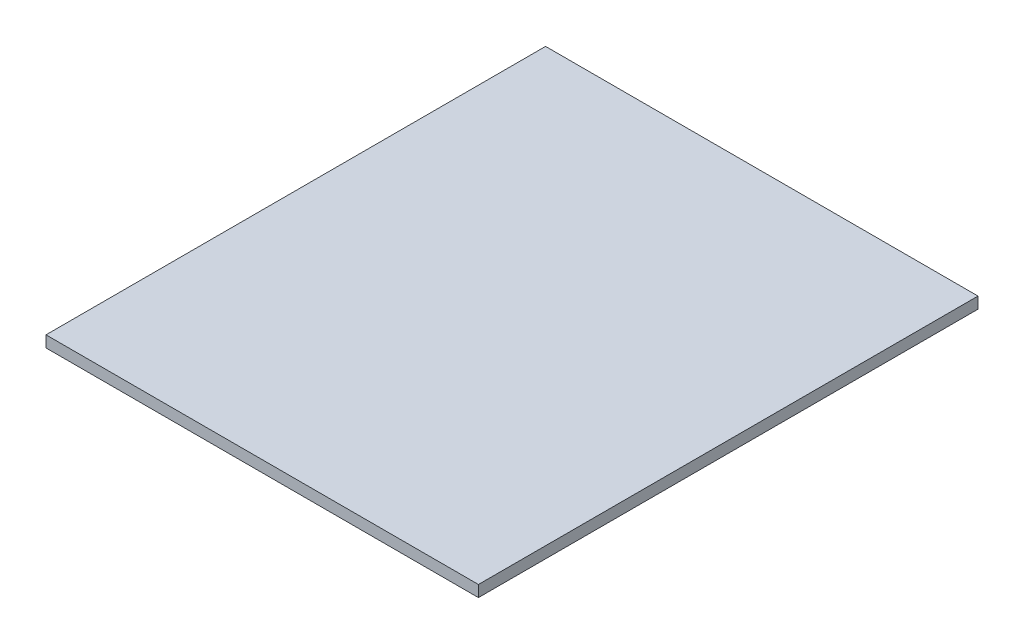
SolidWorks part; units mm, degrees
material "6061 Alloy"
ref_plane "Front Plane" through (0, 0, 0) normal (0, 0, 1) x (1, 0, 0)
ref_plane "Top Plane" through (0, 0, 0) normal (0, 1, 0) x (1, 0, 0)
ref_plane "Right Plane" through (0, 0, 0) normal (1, 0, 0) x (0, 0, -1)
sketch "Sketch1" plane through (0, 0, 0) normal (0, 1, 0) x (1, 0, 0)
  line L1 (-190, -219.5) -> (190, -219.5)
  line L2 (-190, -219.5) -> (-190, 219.5)
  line L3 (-190, 219.5) -> (190, 219.5)
  line L4 (190, -219.5) -> (190, 219.5)
  line L5 (-190, -219.5) -> (190, 219.5) construction
  line L6 (-190, 219.5) -> (190, -219.5) construction
  point P0 (0, 0)
  dimension "D1" = 380
  dimension "D2" = 439
extrude "Boss-Extrude1" add sketch "Sketch1" along normal blind 10
